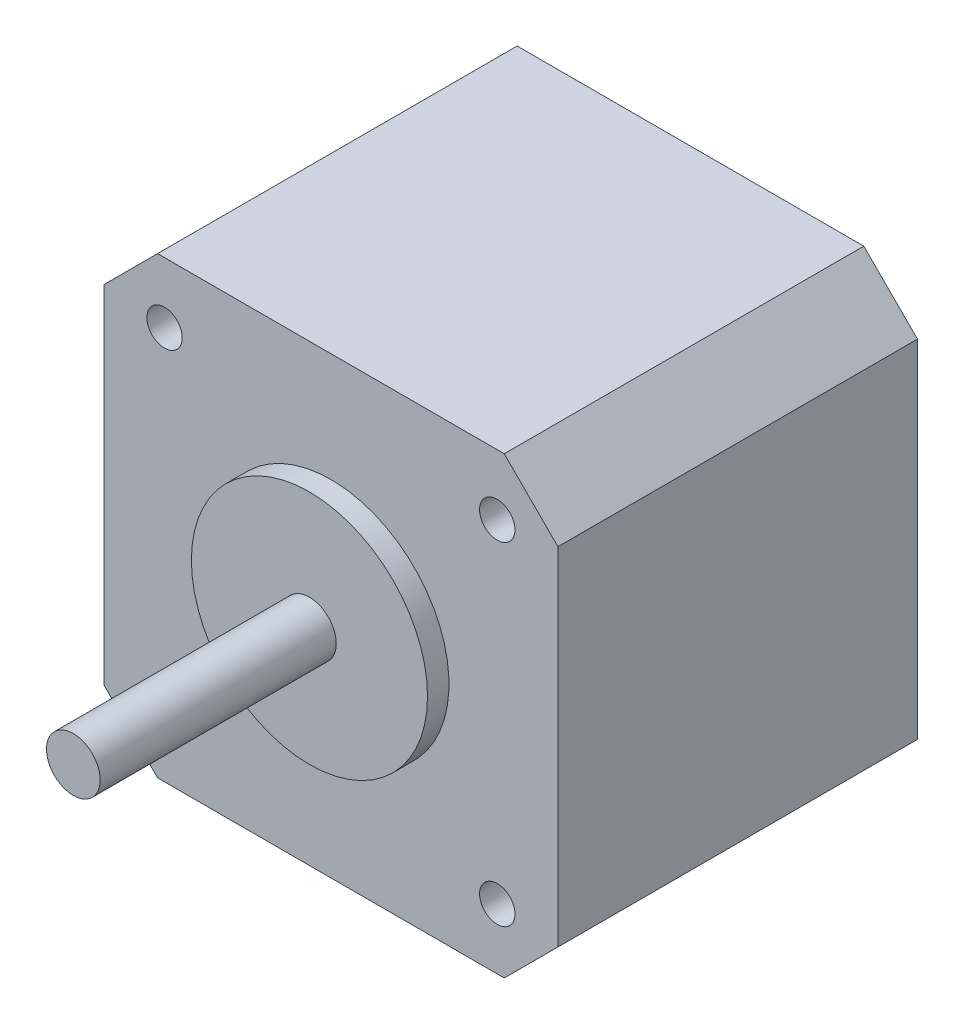
SolidWorks part; units mm, degrees
ref_plane "Front Plane" through (0, 0, 0) normal (0, 0, 1) x (1, 0, 0)
ref_plane "Top Plane" through (0, 0, 0) normal (0, 1, 0) x (1, 0, 0)
ref_plane "Right Plane" through (0, 0, 0) normal (1, 0, 0) x (0, 0, -1)
sketch "Sketch1" plane through (0, 0, 0) normal (0, 0, 1) x (1, 0, 0)
  line L1 (0, 0) -> (42.3, 0)
  line L2 (0, 0) -> (0, 42.3)
  line L3 (0, 42.3) -> (42.3, 42.3)
  line L4 (42.3, 0) -> (42.3, 42.3)
  dimension "D1" = 42.3
  dimension "D2" = 42.3
extrude "Boss-Extrude1" add sketch "Sketch1" along normal blind 33.5
sketch "Sketch2" plane through (0, 0, 33.5) normal (0, 0, 1) x (1, 0, 0)
  line L0 (42.3, 42.3) -> (0, 42.3) construction
  line L1 (21.15, 42.3) -> (21.15, 0) construction
  line L2 (0, 0) -> (42.3, 0) construction
  line L3 (0, 21.15) -> (42.3, 21.15) construction
  line L4 (0, 42.3) -> (0, 0) construction
  line L5 (42.3, 0) -> (42.3, 42.3) construction
  circle A0 centre (5.65, 36.65) radius 1.65
  circle A4 centre (36.65, 36.65) radius 1.65
  circle A5 centre (5.65, 5.65) radius 1.65
  circle A6 centre (36.65, 5.65) radius 1.65
  dimension "D1" = 15.5
  dimension "D3" = 3.3
  dimension "D2" = 15.5
  dimension "D5" = 2
  dimension "D6" = 2
  dimension "D7" = 2
extrude "Cut-Extrude1" cut sketch "Sketch2" against normal blind 10
sketch "Sketch3" plane through (0, 0, 33.5) normal (0, 0, 1) x (1, 0, 0)
  line L0 (21.15, 42.3) -> (21.15, 0) construction
  line L1 (42.3, 42.3) -> (0, 42.3) construction
  line L2 (0, 0) -> (42.3, 0) construction
  circle A0 centre (21.15, 21.15) radius 11
  dimension "D1" = 22
extrude "Boss-Extrude2" add sketch "Sketch3" along normal blind 2
sketch "Sketch4" plane through (0, 0, 35.5) normal (0, 0, 1) x (1, 0, 0)
  circle A0 centre (21.15, 21.15) radius 2.5
  dimension "D1" = 5
extrude "Boss-Extrude3" add sketch "Sketch4" along normal blind 22 and the other way blind 45
sketch "Sketch5" plane through (0, 0, 0) normal (0, 0, -1) x (-1, 0, 0)
  line L0 (0, 0) -> (-42.3, 0) construction
  line L1 (-31.8, 0) -> (-10.5, 0)
  line L2 (-31.8, 0) -> (-31.8, -2.8)
  line L3 (-31.8, -2.8) -> (-10.5, -2.8)
  line L4 (-10.5, 0) -> (-10.5, -2.8)
  line L5 (-42.3, 42.3) -> (0, 42.3) construction
  point P6 (-21.15, 42.3)
  dimension "D1" = 2.8
  dimension "D2" = 21.3
  dimension "D3" = 10.65
extrude "Boss-Extrude4" add sketch "Sketch5" against normal blind 7.15
chamfer "Chamfer1" distance 5 distance2 5 4 edges at (0, 0, 16.75) (42.3, 0, 16.75) (42.3, 42.3, 16.75) (0, 42.3, 16.75)
